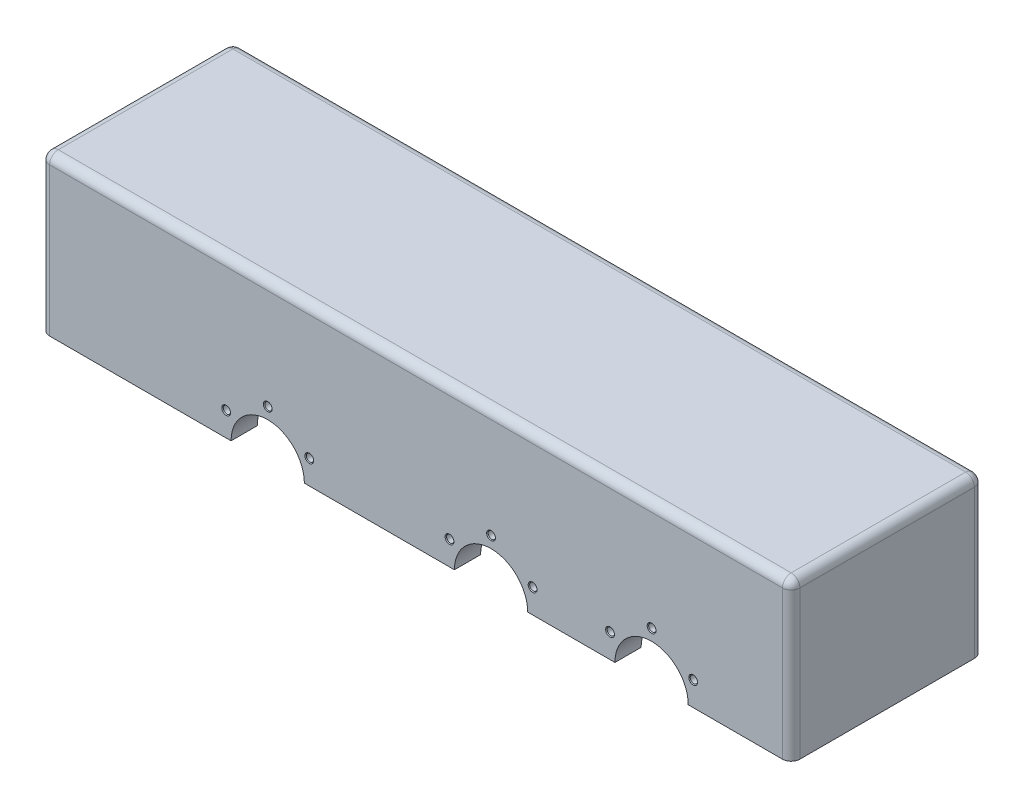
SolidWorks part; units mm, degrees
ref_plane "Front Plane" through (0, 0, 0) normal (0, 0, 1) x (1, 0, 0)
ref_plane "Top Plane" through (0, 0, 0) normal (0, 1, 0) x (1, 0, 0)
ref_plane "Right Plane" through (0, 0, 0) normal (1, 0, 0) x (0, 0, -1)
sketch "Sketch1" plane through (0, 0, 0) normal (0, 1, 0) x (1, 0, 0)
  line L1 (-215, -55) -> (215, -55)
  line L2 (-215, -55) -> (-215, 55)
  line L3 (-215, 55) -> (215, 55)
  line L4 (215, -55) -> (215, 55)
  line L5 (-215, -55) -> (215, 55) construction
  line L6 (-215, 55) -> (215, -55) construction
  line L7 (-200, -40) -> (200, -40)
  line L8 (-200, -40) -> (-200, 40)
  line L9 (-200, 40) -> (200, 40)
  line L10 (200, -40) -> (200, 40)
  line L11 (-200, -40) -> (200, 40) construction
  line L12 (-200, 40) -> (200, -40) construction
  point P0 (0, 0)
  point P6 (0, 0)
  dimension "D1" = 15
  dimension "D2" = 15
  dimension "D3" = 430
  dimension "D4" = 110
extrude "Boss-Extrude1" add sketch "Sketch1" along normal blind 80
sketch "Sketch2" plane through (0, 80, 0) normal (0, 1, 0) x (1, 0, 0)
  line L1 (-215, -55) -> (215, -55)
  line L2 (-215, -55) -> (-215, 55)
  line L3 (-215, 55) -> (215, 55)
  line L4 (215, -55) -> (215, 55)
  line L5 (-215, -55) -> (215, 55) construction
  line L6 (-215, 55) -> (215, -55) construction
  point P0 (0, 0)
extrude "Boss-Extrude2" add sketch "Sketch2" along normal blind 10
sketch "Sketch3" plane through (0, 0, 55) normal (0, 0, 1) x (1, 0, 0)
  line L0 (-215, 0) -> (215, 0) construction
  line L1 (215, 90) -> (215, 0) construction
  circle A0 centre (135, 0) radius 21
  circle A1 centre (43, 0) radius 21
  circle A2 centre (-85, 0) radius 21
  dimension "D1" = 42
  dimension "D4" = 128
  dimension "D2" = 80
  dimension "D3" = 92
extrude "Cut-Extrude1" cut sketch "Sketch3" against normal blind 196
fillet "Fillet1" radius 5 16 edges at (-200, 40, -40) (200, 40, -40) (0, 80, -40) (200, 80, 0) (200, 40, 40) (-200, 80, 0) (0, 80, 40) (-200, 40, 40) (215, 45, 55) (215, 45, -55) (215, 90, 0) (0, 90, 55) (-215, 45, 55) (-215, 90, 0) (0, 90, -55) (-215, 45, -55)
sketch "Sketch4" plane through (0, 0, -55) normal (0, 0, -1) x (-1, 0, 0)
  line L0 (-135, 0) -> (-158.8157, 13.75) construction
  line L1 (-43, 0) -> (-66.8157, 13.75) construction
  line L2 (85, 0) -> (61.1843, 13.75) construction
  line L3 (-210, 0) -> (-156, 0) construction
  line L4 (-114, 0) -> (-64, 0) construction
  line L5 (-22, 0) -> (64, 0) construction
  circle A0 centre (-135, 0) radius 27.5 construction
  circle A1 centre (-43, 0) radius 27.5 construction
  circle A2 centre (85, 0) radius 27.5 construction
  dimension "D4" = 55
  dimension "D1" = 30
  dimension "D2" = 30
  dimension "D3" = 30
hole_wizard "M5 Tapped Hole1" positions "3DSketch2" profile "Sketch6" tap size "M5" standard "ISO"
sketch3d "3DSketch2"
  point P0 (158.8157, 13.75, -55)
cosmetic thread "Hole Thread1" parameters "D1"=10, "D2"=5
sketch "Sketch6" plane through (158.8157, 13.75, -55) normal (1, 0, 0) x (0, 1, 0)
  line L0 (0, 0) -> (0, 13.6618)
  line L1 (0, 13.6618) -> (2.1, 12.4)
  line L2 (2.1, 12.4) -> (2.1, 0.425)
  line L3 (2.1, 0.425) -> (2.525, 0)
  line L5 (2.525, 0) -> (0, 0)
  line L6 (-2.1, 0.425) -> (-2.525, 0) construction
  line L10 (0, 13.6618) -> (-2.1, 12.4) construction
  line L11 (0, -6.35) -> (0, 107.95) construction
  dimension "Tap Drill Dia." = 4.2
  dimension "Tap Drill Depth" = 12.4
  dimension "Near C'Sink Dia." = 5.05
  dimension "Near C'Sink Angle" = 90
  dimension "Drill Angle" = 118
hole_wizard "M5 Tapped Hole2" positions "3DSketch3" profile "Sketch7" tap size "M5" standard "ISO"
sketch3d "3DSketch3"
  point P0 (66.8157, 13.75, -55)
sketch "Sketch7" plane through (66.8157, 13.75, -55) normal (1, 0, 0) x (0, 1, 0)
  line L0 (0, 0) -> (0, 13.6618)
  line L1 (0, 13.6618) -> (2.1, 12.4)
  line L2 (2.1, 12.4) -> (2.1, 0.425)
  line L3 (2.1, 0.425) -> (2.525, 0)
  line L5 (2.525, 0) -> (0, 0)
  line L6 (-2.1, 0.425) -> (-2.525, 0) construction
  line L10 (0, 13.6618) -> (-2.1, 12.4) construction
  line L11 (0, -6.35) -> (0, 107.95) construction
  dimension "Tap Drill Dia." = 4.2
  dimension "Tap Drill Depth" = 12.4
  dimension "Near C'Sink Dia." = 5.05
  dimension "Near C'Sink Angle" = 90
  dimension "Drill Angle" = 118
cosmetic thread "Hole Thread2" parameters "D1"=10, "D2"=5
hole_wizard "M5 Tapped Hole3" positions "3DSketch6" profile "Sketch10" tap size "M5" standard "ISO"
sketch3d "3DSketch6"
  point P0 (-61.1843, 13.75, -55)
sketch "Sketch10" plane through (-61.1843, 13.75, -55) normal (1, 0, 0) x (0, 1, 0)
  line L0 (0, 0) -> (0, 13.6618)
  line L1 (0, 13.6618) -> (2.1, 12.4)
  line L2 (2.1, 12.4) -> (2.1, 0.425)
  line L3 (2.1, 0.425) -> (2.525, 0)
  line L5 (2.525, 0) -> (0, 0)
  line L6 (-2.1, 0.425) -> (-2.525, 0) construction
  line L10 (0, 13.6618) -> (-2.1, 12.4) construction
  line L11 (0, -6.35) -> (0, 107.95) construction
  dimension "Tap Drill Dia." = 4.2
  dimension "Tap Drill Depth" = 12.4
  dimension "Near C'Sink Dia." = 5.05
  dimension "Near C'Sink Angle" = 90
  dimension "Drill Angle" = 118
cosmetic thread "Hole Thread3" parameters "D1"=10, "D2"=5
pattern_circular "CirPattern1" count 6 over 360 about axis through (135, 0, 0) along (0, 0, 1) skipping 3, 4, 5 of "M5 Tapped Hole1"
cosmetic thread "Hole Thread4" parameters "D1"=10, "D2"=5
cosmetic thread "Hole Thread5" parameters "D1"=10, "D2"=5
pattern_circular "CirPattern2" count 6 over 360 about axis through (43, 0, -141) along (0, 0, 1) skipping 1, 2, 3 of "M5 Tapped Hole2"
cosmetic thread "Hole Thread6" parameters "D1"=10, "D2"=5
cosmetic thread "Hole Thread7" parameters "D1"=10, "D2"=5
pattern_circular "CirPattern3" count 6 over 360 about axis through (-85, 0, 0) along (0, 0, 1) skipping 3, 4, 5 of "M5 Tapped Hole3"
cosmetic thread "Hole Thread8" parameters "D1"=10, "D2"=5
cosmetic thread "Hole Thread9" parameters "D1"=10, "D2"=5
mirror "Mirror1" about plane through (0, 0, 0) normal (0, 0, 1) of "CirPattern1", "CirPattern2", "CirPattern3", "M5 Tapped Hole1", "M5 Tapped Hole2", "M5 Tapped Hole3"
cosmetic thread "Hole Thread10" parameters "D1"=10, "D2"=5
cosmetic thread "Hole Thread11" parameters "D1"=10, "D2"=5
cosmetic thread "Hole Thread12" parameters "D1"=10, "D2"=5
cosmetic thread "Hole Thread13" parameters "D1"=10, "D2"=5
cosmetic thread "Hole Thread14" parameters "D1"=10, "D2"=5
cosmetic thread "Hole Thread15" parameters "D1"=10, "D2"=5
cosmetic thread "Hole Thread16" parameters "D1"=10, "D2"=5
cosmetic thread "Hole Thread17" parameters "D1"=10, "D2"=5
cosmetic thread "Hole Thread18" parameters "D1"=10, "D2"=5
